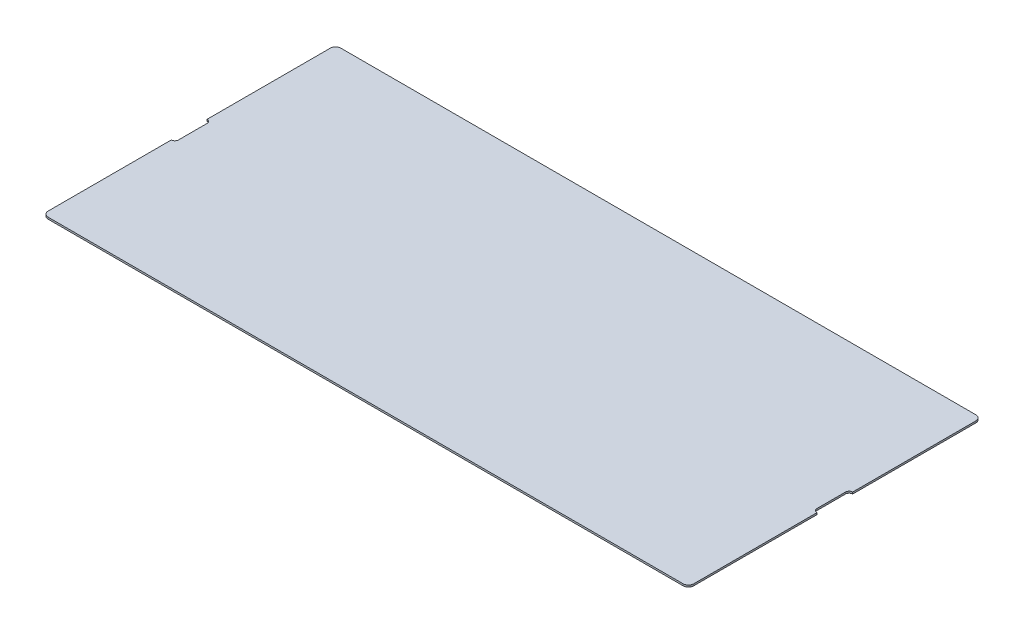
SolidWorks part; units mm, degrees
ref_plane "Front Plane" through (0, 0, 0) normal (0, 0, 1) x (1, 0, 0)
ref_plane "Top Plane" through (0, 0, 0) normal (0, 1, 0) x (1, 0, 0)
ref_plane "Right Plane" through (0, 0, 0) normal (1, 0, 0) x (0, 0, -1)
sketch "Sketch1" plane through (0, 0, 0) normal (0, 1, 0) x (1, 0, 0)
  line L0 (-90.2, 0) -> (90.2, 0) construction
  line L1 (-88.7, 40.9) -> (88.7, 40.9)
  line L2 (-90.2, 39.4) -> (-90.2, -39.4)
  line L3 (-88.7, -40.9) -> (88.7, -40.9)
  line L4 (90.2, 39.4) -> (90.2, -39.4)
  line L5 (-90.2, 40.9) -> (90.2, -40.9) construction
  line L6 (-90.2, -40.9) -> (90.2, 40.9) construction
  line L7 (-90.2, 4) -> (-90.2, -4) construction
  line L8 (-89.2, 4) -> (-89.2, -4)
  line L9 (-91.2, 4) -> (-91.2, -4)
  line L10 (0, 40.9) -> (0, -40.9) construction
  line L11 (90.2, 4) -> (90.2, -4) construction
  line L12 (89.2, 4) -> (89.2, -4)
  line L13 (91.2, 4) -> (91.2, -4)
  arc A0 (88.7, -40.9) -> (90.2, -39.4) centre (88.7, -39.4) ccw
  arc A1 (88.7, 40.9) -> (90.2, 39.4) centre (88.7, 39.4) cw
  arc A2 (-90.2, -39.4) -> (-88.7, -40.9) centre (-88.7, -39.4) ccw
  arc A3 (-88.7, 40.9) -> (-90.2, 39.4) centre (-88.7, 39.4) ccw
  arc A4 (-89.2, 4) -> (-91.2, 4) centre (-90.2, 4) ccw
  arc A5 (-91.2, -4) -> (-89.2, -4) centre (-90.2, -4) ccw
  arc A6 (89.2, 4) -> (91.2, 4) centre (90.2, 4) cw
  arc A7 (91.2, -4) -> (89.2, -4) centre (90.2, -4) cw
  point P0 (0, 0)
  point P22 (-90.2, 0)
  point P31 (90.2, 0)
  dimension "D3" = 1.5
  dimension "D1" = 81.8
  dimension "D2" = 180.4
  dimension "D4" = 8
  dimension "D5" = 2
extrude "Shape" add sketch "Sketch1" along normal blind 0.5 contours L4 A7 L12 A6 A1 L1 A3 L2 A4 L8 A5 A2 L3 A0
